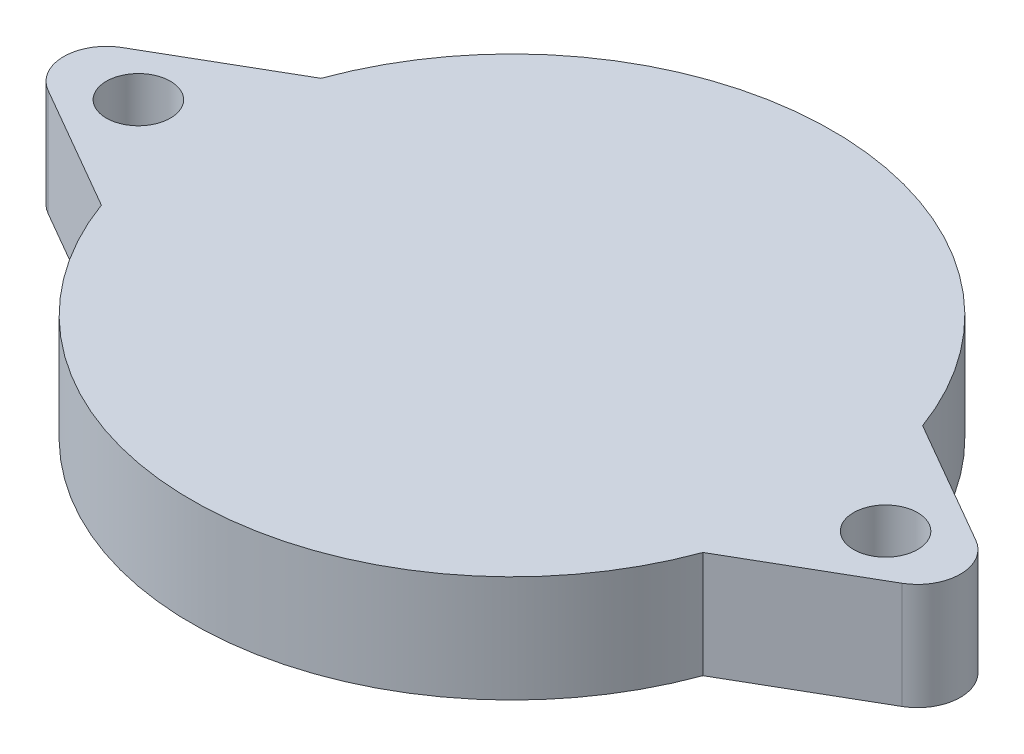
SolidWorks part; units mm, degrees
ref_plane "前基準面" through (0, 0, 0) normal (0, 0, 1) x (1, 0, 0)
ref_plane "上基準面" through (0, 0, 0) normal (0, 1, 0) x (1, 0, 0)
ref_plane "右基準面" through (0, 0, 0) normal (1, 0, 0) x (0, 0, -1)
sketch "草圖1" plane through (0, 0, 0) normal (0, 1, 0) x (1, 0, 0)
  line L0 (-43.5054, -109.4733) -> (95.5784, -154.3962) construction
  line L1 (0, 0) -> (0, 150)
  line L2 (0, 115.6188) -> (0, 104.1566) construction
  line L3 (87.3057, 0) -> (151.3702, 0) construction
  line L4 (-14.0904, 5.144) -> (-20, 1.7321)
  line L5 (-14.0904, -5.144) -> (-20, -1.7321)
  line L6 (14.0904, 5.144) -> (20, 1.7321)
  line L7 (14.0904, -5.144) -> (20, -1.7321)
  circle A0 centre (0, 0) radius 15
  circle A1 centre (-17.5, 0) radius 1.5
  circle A2 centre (17.5, 0) radius 1.5
  arc A3 (-20, 1.7321) -> (-20, -1.7321) centre (-19, 0) ccw
  arc A4 (20, 1.7321) -> (20, -1.7321) centre (19, 0) cw
  point P11 (0, 0)
  point P16 (0, 0)
  point P20 (-21.4507, -1.2708)
  point P21 (-21.0779, 0)
  point P22 (-13.986, 5.4213)
  point P29 (-20.1306, 1.7321)
  dimension "D2" = 30
  dimension "D3" = 3
  dimension "D5" = 60
  dimension "D6" = 2
  dimension "D1" = 150
  dimension "D4" = 35
  dimension "D7" = 38
extrude "填料-伸長1" add sketch "草圖1" along normal blind 5
